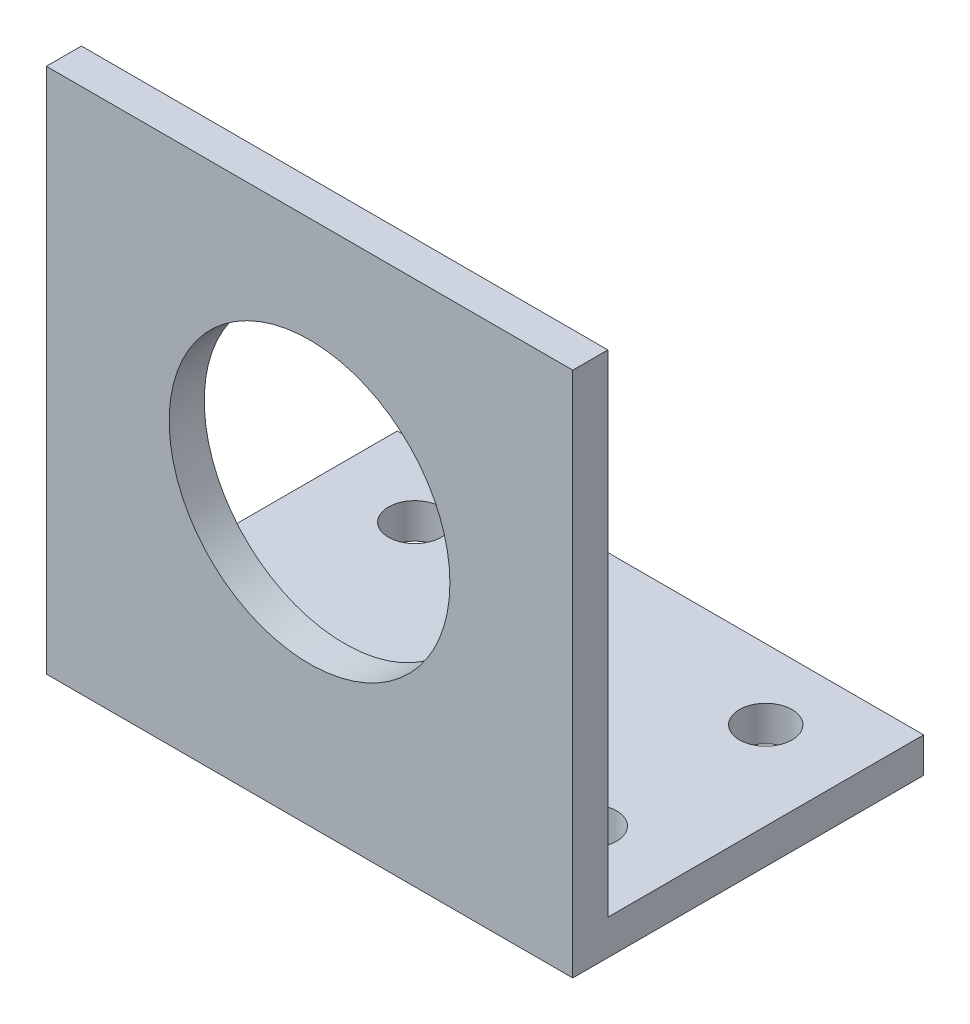
SolidWorks part; units mm, degrees
material "6063-O"
ref_plane "Front" through (0, 0, 0) normal (0, 0, 1) x (1, 0, 0)
ref_plane "Top" through (0, 0, 0) normal (0, 1, 0) x (1, 0, 0)
ref_plane "Right" through (0, 0, 0) normal (1, 0, 0) x (0, 0, -1)
sketch "草图1" plane through (0, 0, 0) normal (1, 0, 0) x (0, 0, -1)
  line L0 (0, 0) -> (0, 38)
  line L1 (0, 38) -> (3, 38)
  line L2 (3, 38) -> (3, 3)
  line L3 (3, 3) -> (38, 3)
  line L4 (38, 3) -> (38, 0)
  line L5 (38, 0) -> (0, 0)
  dimension "D1" = 38
  dimension "D2" = 3
  dimension "D3" = 35
  dimension "D4" = 35
extrude "凸台-拉伸1" add sketch "草图1" along normal blind 20
ref_plane "基准面1" through (20, 3, -38) normal (-1, 0, 0) x (0, 0, 1)
sketch "草图9" plane through (20, 0, 0) normal (1, 0, 0) x (0, 0, -1)
  line L0 (0, 0) -> (38, 0) construction
  line L1 (0, 38) -> (3, 38)
  line L2 (0, 38) -> (0, 0)
  line L3 (0, 0) -> (3, 0)
  line L4 (3, 38) -> (3, 0)
  line L6 (3, 3) -> (38, 3)
  line L7 (3, 3) -> (3, 0)
  line L8 (3, 0) -> (38, 0)
  line L9 (38, 3) -> (38, 0)
  line M1 (0, 0) -> (38, 0)
  line M2 (38, 0) -> (38, 3)
  line M3 (38, 3) -> (3, 3)
  line M4 (3, 3) -> (3, 38)
  line M5 (3, 38) -> (0, 38)
  line M6 (0, 38) -> (0, 0)
extrude "凸台-拉伸2" add sketch "草图9" along normal blind 5 contours L4 M4 M5 M6 M1 | L4 M3 M1 M2
sketch "草图10" plane through (0, 0, 0) normal (-1, 0, 0) x (0, 0, 1)
  line L1 (0, 38) -> (-3, 38)
  line L2 (0, 38) -> (0, 3)
  line L3 (0, 3) -> (-3, 3)
  line L4 (-3, 38) -> (-3, 3)
  line L5 (0, 3) -> (-38, 3)
  line L6 (0, 3) -> (0, 0)
  line L7 (0, 0) -> (-38, 0)
  line L8 (-38, 3) -> (-38, 0)
  line M1 (-38, 0) -> (0, 0)
  line M2 (0, 0) -> (0, 38)
  line M3 (0, 38) -> (-3, 38)
  line M4 (-3, 38) -> (-3, 3)
  line M5 (-3, 3) -> (-38, 3)
  line M6 (-38, 3) -> (-38, 0)
extrude "凸台-拉伸3" add sketch "草图10" along normal blind 5 contours L3 M2 M3 M4 | L3 M2 M5 M6 M1
sketch "草图11" plane through (0, 0, 0) normal (0, 0, 1) x (1, 0, 0)
  line L0 (25, 0) -> (-5, 0) construction
  line L2 (25, 38) -> (25, 0) construction
  circle A0 centre (10, 16) radius 8
  dimension "D2" = 16
  dimension "D1" = 16
  dimension "D3" = 15
extrude "切除-拉伸4" cut sketch "草图11" against normal blind 8
sketch "草图12" plane through (0, 0, -38) normal (0, 0, -1) x (-1, 0, 0)
  line L0 (-25, 0) -> (-25, 3) construction
  line L1 (-25, 3) -> (5, 3)
  line L2 (-25, 3) -> (-25, 0)
  line L3 (-25, 0) -> (5, 0)
  line L4 (5, 3) -> (5, 0)
  line L5 (-25, 0) -> (5, 0) construction
extrude "切除-拉伸5" cut sketch "草图12" against normal blind 18
sketch "草图13" plane through (0, 3, 0) normal (0, 1, 0) x (1, 0, 0)
  line L0 (-5, 20) -> (25, 20) construction
  line L1 (-5, 20) -> (25, 20)
  line L2 (-5, 20) -> (-5, 3)
  line L3 (-5, 3) -> (25, 3)
  line L4 (25, 20) -> (25, 3)
  line L5 (25, 20) -> (25, 3) construction
extrude "切除-拉伸6" cut sketch "草图13" against normal blind 1
sketch "草图14" plane through (0, 0, -3) normal (0, 0, -1) x (-1, 0, 0)
  line L0 (5, 2) -> (-25, 2) construction
  line L1 (-25, 2) -> (5, 2)
  line L2 (-25, 2) -> (-25, 38)
  line L3 (-25, 38) -> (5, 38)
  line L4 (5, 2) -> (5, 38)
  line L5 (-25, 38) -> (-25, 2) construction
  line L6 (5, 38) -> (5, 2) construction
  line L7 (-25, 38) -> (5, 38) construction
extrude "切除-拉伸7" cut sketch "草图14" against normal blind 1
sketch "草图15" plane through (0, 2, 0) normal (0, 1, 0) x (1, 0, 0)
  line L0 (-5, 20) -> (-5, 2) construction
  line L1 (25, 2) -> (25, 20) construction
  line L2 (25, 2) -> (-5, 2) construction
  line L3 (25, 20) -> (-5, 20) construction
  circle A0 centre (20, 6) radius 1.5
  circle A1 centre (0, 6) radius 1.5
  circle A2 centre (0, 16) radius 1.5
  circle A3 centre (20, 16) radius 1.5
  dimension "D9" = 3
  dimension "D10" = 3
  dimension "D11" = 3
  dimension "D12" = 3
  dimension "D1" = 5
  dimension "D2" = 5
  dimension "D3" = 5
  dimension "D4" = 5
  dimension "D5" = 4
  dimension "D6" = 4
  dimension "D7" = 4
  dimension "D8" = 4
extrude "切除-拉伸8" cut sketch "草图15" against normal blind 2
sketch "草图17" plane through (0, 38, 0) normal (0, 1, 0) x (1, 0, 0)
  line L1 (-11.4607, -1.4262) -> (27.8926, -1.4262)
  line L2 (-11.4607, -1.4262) -> (-11.4607, 4.2768)
  line L3 (-11.4607, 4.2768) -> (27.8926, 4.2768)
  line L4 (27.8926, -1.4262) -> (27.8926, 4.2768)
extrude "切除-拉伸9" cut sketch "草图17" against normal blind 8
